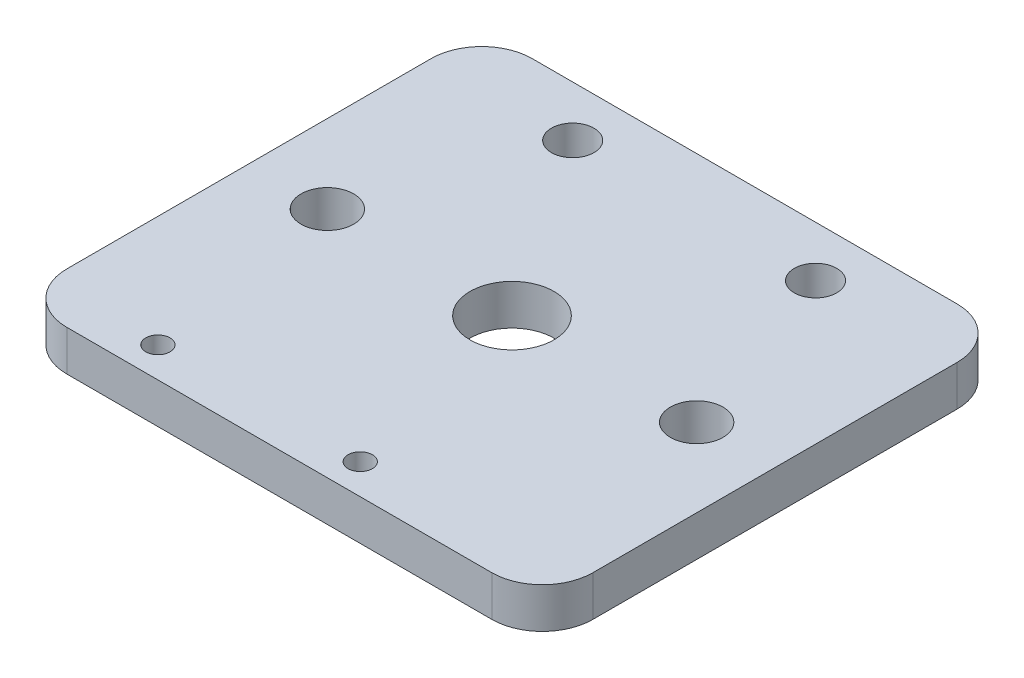
SolidWorks part; units mm, degrees
material "6061 合金"
ref_plane "前视基准面" through (0, 0, 0) normal (0, 0, 1) x (1, 0, 0)
ref_plane "上视基准面" through (0, 0, 0) normal (0, 1, 0) x (1, 0, 0)
ref_plane "右视基准面" through (0, 0, 0) normal (1, 0, 0) x (0, 0, -1)
sketch "草图1" plane through (0, 0, 0) normal (0, 1, 0) x (1, 0, 0)
  line L1 (-26, -23) -> (26, -23)
  line L2 (-26, -23) -> (-26, 23)
  line L3 (-26, 23) -> (26, 23)
  line L4 (26, -23) -> (26, 23)
  line L5 (0, 23) -> (0, -23) construction
  line L6 (-26, 0) -> (26, 0) construction
  circle A0 centre (-18.25, 0) radius 2.6
  circle A1 centre (18.25, 0) radius 2.6
  circle A2 centre (0, 0) radius 4.15
  point P0 (0, 0)
  dimension "D3" = 36.5
  dimension "D4" = 5.2
  dimension "D5" = 8.3
  dimension "D1" = 52
  dimension "D2" = 46
extrude "主板" add sketch "草图1" along normal blind 4
sketch "草图4" plane through (0, 4, 0) normal (0, 1, 0) x (1, 0, 0)
  line L0 (0, -1000) -> (0, 49000) construction
  line L1 (-1000, 0) -> (49000, 0) construction
  line L2 (-1020.8031, 18) -> (48979.1969, 18) construction
  line L4 (26, 23) -> (-26, 23) construction
  circle A0 centre (-12, 18) radius 2.1
  circle A1 centre (12, 18) radius 2.1
  circle A2 centre (12, -18) radius 2.1
  circle A3 centre (-12, -18) radius 2.1
  dimension "D2" = 4.2
  dimension "D3" = 24
  dimension "D1" = 5
extrude "垂直板接件" cut sketch "草图4" against normal through all
sketch "草图6" plane through (0, 4, 0) normal (0, 1, 0) x (1, 0, 0)
  circle A0 centre (-12, -18) radius 2.1
  circle A1 centre (12, -18) radius 2.1
  dimension "D1" = 4.2
  dimension "D2" = 4.2
extrude "凸台-拉伸1" add sketch "草图6" against normal blind 4
sketch "草图7" plane through (0, 4, 0) normal (0, 1, 0) x (1, 0, 0)
  circle A0 centre (5, -20) radius 1.2
  circle A1 centre (-15, -20) radius 1.2
  dimension "D1" = 2.4
  dimension "D2" = 2.4
extrude "切除-拉伸1" cut sketch "草图7" against normal through all
sketch "草图8" plane through (0, 0, 0) normal (0, -1, 0) x (1, 0, 0)
  line L0 (26, -23) -> (55.3847, -23)
  line L1 (26, -23) -> (26, 23)
  line L2 (26, 23) -> (55.3847, 23)
  line L3 (55.3847, 23) -> (55.3847, -23)
extrude "凸台-拉伸2" add sketch "草图8" against normal up to surface (4 mm away) up to face at (5, 4, 21.2)
sketch "草图9" plane through (0, 4, 0) normal (0, 1, 0) x (1, 0, 0)
  line L0 (55.3847, 23) -> (26, 23)
  line L1 (55.3847, 23) -> (-26, 23) construction
  line L2 (26, 18) -> (26, -18) construction
  line L3 (26, 23) -> (26, -23)
  line L4 (-26, -23) -> (55.3847, -23) construction
  line L5 (26, -23) -> (26, -26) construction
  line L6 (26, -23) -> (55.3847, -23)
  line L7 (55.3847, -23) -> (55.3847, 23)
extrude "切除-拉伸2" cut sketch "草图9" against normal through all
fillet "圆角1" radius 5 4 edges at (-26, 2, -23) (-26, 2, 23) (26, 2, 23) (26, 2, -23)
